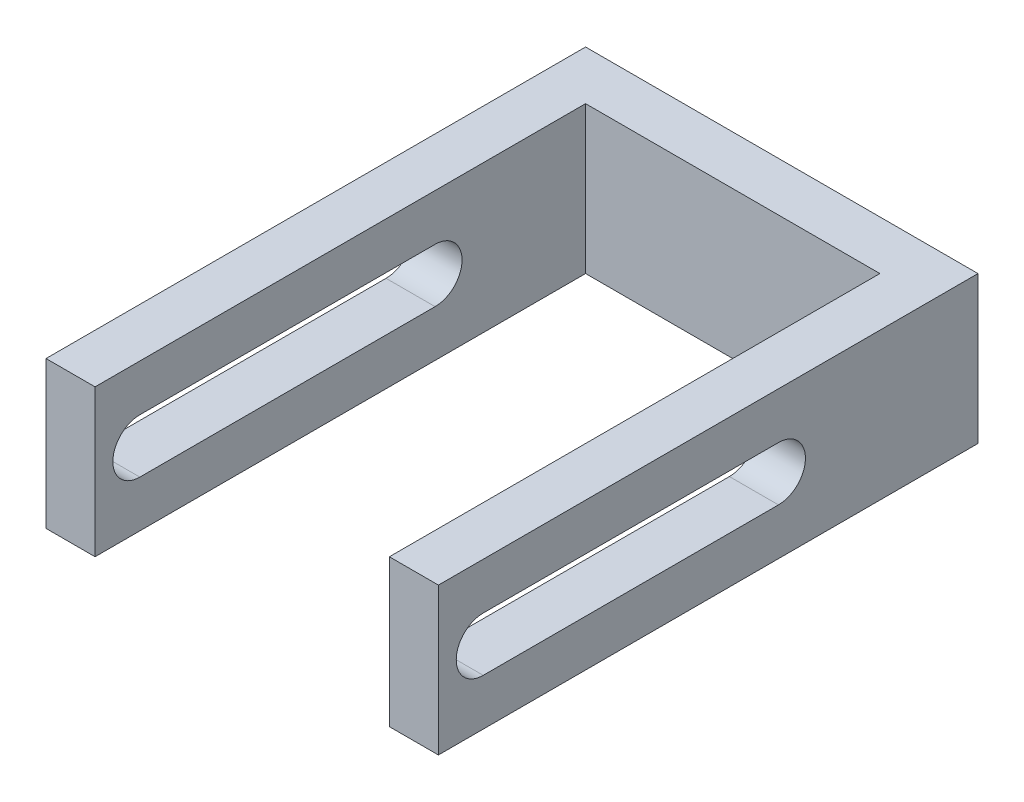
SolidWorks part; units mm, degrees
ref_plane "Front Plane" through (0, 0, 0) normal (0, 0, 1) x (1, 0, 0)
ref_plane "Top Plane" through (0, 0, 0) normal (0, 1, 0) x (1, 0, 0)
ref_plane "Right Plane" through (0, 0, 0) normal (1, 0, 0) x (0, 0, -1)
sketch "Sketch1" plane through (0, 0, 0) normal (0, 1, 0) x (1, 0, 0)
  line L0 (0, 0) -> (-5, 0)
  line L1 (-5, 0) -> (-5, 55)
  line L2 (-5, 55) -> (23.9655, 55)
  line L3 (23.9655, 55) -> (35, 55)
  line L4 (35, 55) -> (35, 0)
  line L5 (35, 0) -> (30, 0)
  line L6 (30, 0) -> (30, 50)
  line L7 (30, 50) -> (0, 50)
  line L8 (0, 50) -> (0, 0)
  dimension "D1" = 5
  dimension "D2" = 5
  dimension "D3" = 50
  dimension "D4" = 55
  dimension "D5" = 30
extrude "Boss-Extrude1" add sketch "Sketch1" along normal blind 15
sketch "Sketch2" plane through (35, 0, 0) normal (1, 0, 0) x (0, 0, -1)
  line L0 (4.565, 7.5) -> (34.6598, 7.5) construction
  line L1 (4.565, 10.25) -> (34.6598, 10.25)
  line L2 (4.565, 4.75) -> (34.6598, 4.75)
  line L3 (0, 0) -> (55, 0) construction
  arc A0 (4.565, 10.25) -> (4.565, 4.75) centre (4.565, 7.5) ccw
  arc A1 (34.6598, 4.75) -> (34.6598, 10.25) centre (34.6598, 7.5) ccw
  point P2 (19.6124, 7.5)
  point P9 (34.6598, 7.5)
  dimension "D1" = 7.5
  dimension "D2" = 5.5
extrude "Cut-Extrude1" cut sketch "Sketch2" against normal through all
